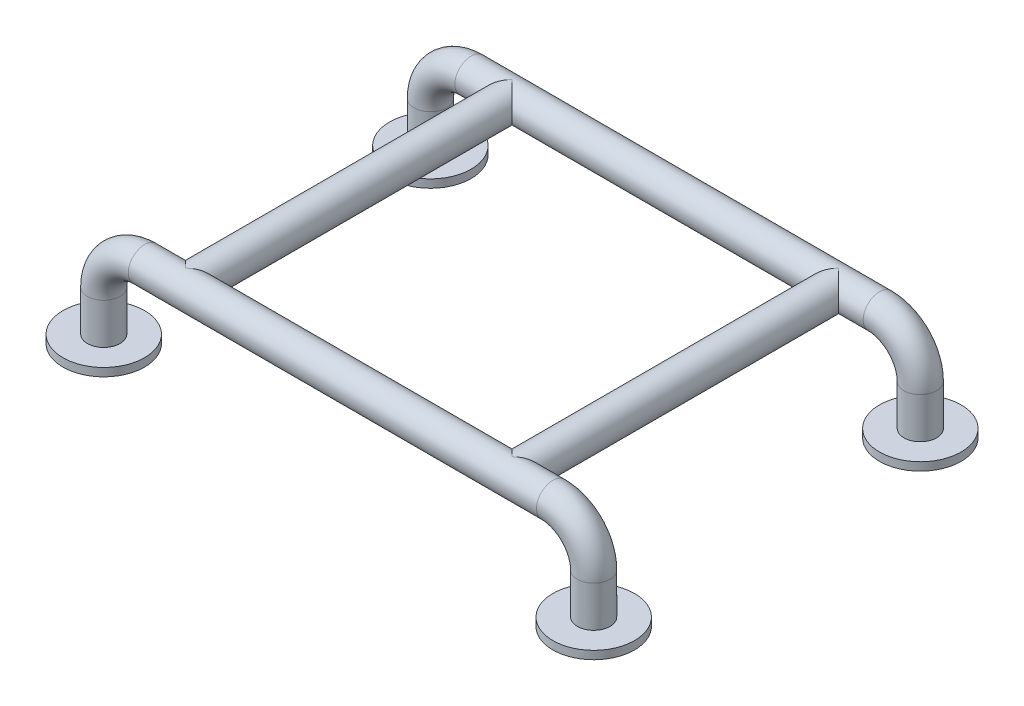
SolidWorks part; units mm, degrees
ref_plane "Front Plane" through (0, 0, 0) normal (0, 0, 1) x (1, 0, 0)
ref_plane "Top Plane" through (0, 0, 0) normal (0, 1, 0) x (1, 0, 0)
ref_plane "Right Plane" through (0, 0, 0) normal (1, 0, 0) x (0, 0, -1)
sketch "Sketch2" plane through (0, 0, 0) normal (0, 0, 1) x (1, 0, 0)
  line L0 (0, 0) -> (0, 50)
  line L1 (50, 100) -> (550, 100)
  line L2 (600, 50) -> (600, 0)
  arc A0 (600, 50) -> (550, 100) centre (550, 50) ccw
  arc A1 (50, 100) -> (0, 50) centre (50, 50) ccw
  point P9 (0, 100)
  dimension "D3" = 50
  dimension "D1" = 600
  dimension "D2" = 100
sketch "Sketch3" plane through (0, 0, 0) normal (0, 1, 0) x (1, 0, 0)
  circle A0 centre (0, 0) radius 20
  dimension "D1" = 40
sweep "Sweep1" add profiles "Sketch3" path "Sketch2"
sketch "Sketch4" plane through (0, 0, 0) normal (0, -1, 0) x (1, 0, 0)
  circle A0 centre (0, 0) radius 50
  circle A1 centre (600, 0) radius 50
  dimension "D1" = 100
extrude "Boss-Extrude1" add sketch "Sketch4" along normal blind 10
ref_plane "Plane1" through (0, 0, 400) normal (0, 0, 1) x (1, 0, 0)
sketch "Sketch5" plane through (0, 0, 400) normal (0, 0, 1) x (1, 0, 0)
  line L0 (0, 0) -> (0, 50)
  line L1 (550, 100) -> (50, 100)
  line L2 (600, 50) -> (600, -10)
  line L3 (550, -10) -> (650, -10) construction
  arc A0 (600, 50) -> (550, 100) centre (550, 50) ccw
  arc A1 (50, 100) -> (0, 50) centre (50, 50) ccw
  point P9 (600, 100)
  point P12 (0, 100)
  dimension "D3" = 50
  dimension "D1" = 100
  dimension "D2" = 600
sketch "Sketch7" plane through (0, 0, 0) normal (0, 1, 0) x (1, 0, 0)
  circle A0 centre (0, -400) radius 20
  dimension "D1" = 40
sweep "Sweep2" add profiles "Sketch7" path "Sketch5"
sketch "Sketch9" plane through (0, 0, 0) normal (0, -1, 0) x (1, 0, 0)
  circle A0 centre (0, 400) radius 50
  circle A1 centre (600, 400) radius 50
  dimension "D1" = 100
extrude "Boss-Extrude2" add sketch "Sketch9" along normal blind 10
ref_plane "Plane2" through (100, 0, 0) normal (1, 0, 0) x (0, 0, -1)
ref_plane "Plane3" through (500, 0, 0) normal (1, 0, 0) x (0, 0, -1)
sketch "Sketch11" plane through (0, 0, 0) normal (0, 0, 1) x (1, 0, 0)
  line L0 (100, -71.5) -> (100, 71.5) construction
  line L1 (550, 120) -> (50, 120) construction
  line L2 (500, -71.5) -> (500, 71.5) construction
  circle A0 centre (100, 100) radius 20
  circle A1 centre (500, 100) radius 20
  dimension "D1" = 40
  dimension "D2" = 40
extrude "Boss-Extrude3" add sketch "Sketch11" along normal blind 400
